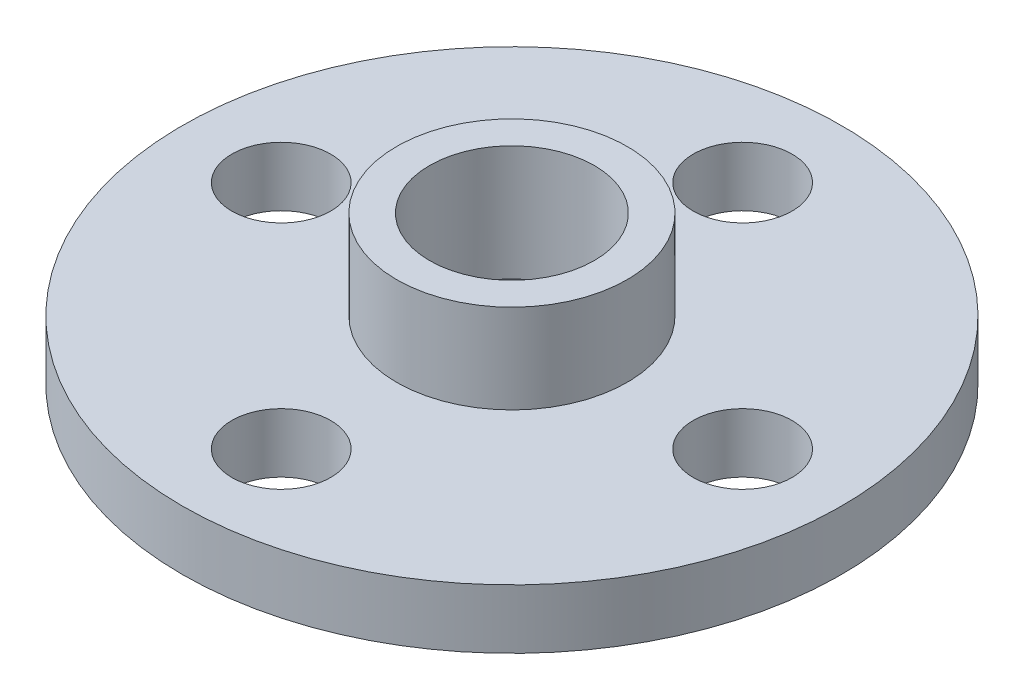
SolidWorks part; units mm, degrees
ref_plane "Front Plane" through (0, 0, 0) normal (0, 0, 1) x (1, 0, 0)
ref_plane "Top Plane" through (0, 0, 0) normal (0, 1, 0) x (1, 0, 0)
ref_plane "Right Plane" through (0, 0, 0) normal (1, 0, 0) x (0, 0, -1)
sketch "Sketch1" plane through (0, 0, 0) normal (0, 1, 0) x (1, 0, 0)
  circle A0 centre (0, 0) radius 10
  circle A1 centre (0, 0) radius 2.5
  circle A2 centre (0, 7) radius 1.5
  circle A3 centre (7, 0) radius 1.5
  circle A4 centre (0, -7) radius 1.5
  circle A5 centre (-7, 0) radius 1.5
  dimension "D1" = 20
  dimension "D2" = 5
  dimension "D3" = 3
  dimension "D4" = 7
  dimension "D5" = 4
extrude "Boss-Extrude1" add sketch "Sketch1" along normal blind 1.8
sketch "Sketch2" plane through (0, 1.8, 0) normal (0, 1, 0) x (1, 0, 0)
  circle A0 centre (0, 0) radius 2.5
  circle A1 centre (0, 0) radius 3.5
  dimension "D1" = 7
extrude "Boss-Extrude2" add sketch "Sketch2" along normal blind 2.7
sketch "Sketch3" plane through (0, 0, 0) normal (0, -1, 0) x (-1, 0, 0)
  circle A0 centre (0, 0) radius 2.5
extrude "Boss-Extrude3" add sketch "Sketch3" against normal blind 1
